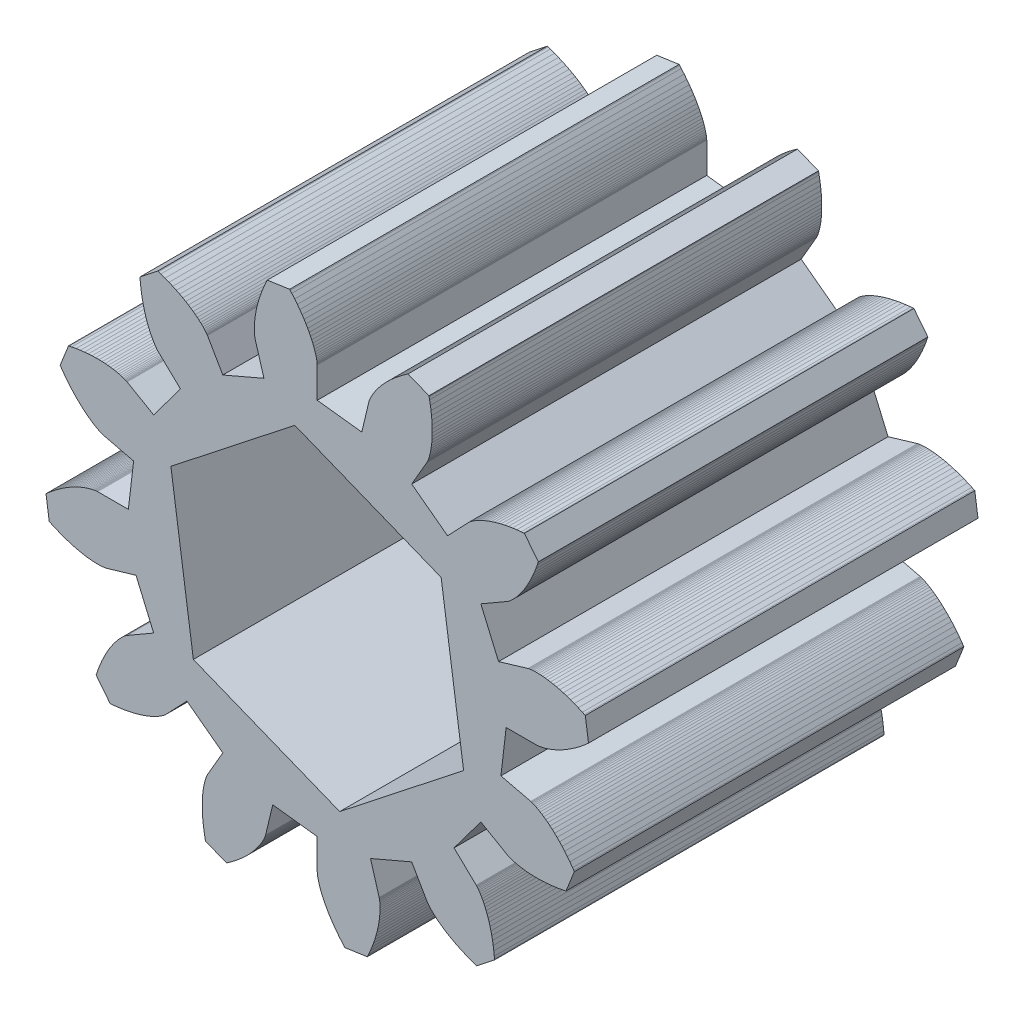
SolidWorks part; units mm, degrees
ref_plane "正面" through (0, 0, 0) normal (0, 0, 1) x (1, 0, 0)
ref_plane "平面" through (0, 0, 0) normal (0, 1, 0) x (1, 0, 0)
ref_plane "右側面" through (0, 0, 0) normal (1, 0, 0) x (0, 0, -1)
sketch "Model" plane through (0, 0, 0) normal (0, 0, 1) x (1, 0, 0)
  line L0 (2.425, 0) -> (2.8195, 0)
  line L1 (2.8195, 0) -> (2.8221, 0.0001)
  line L2 (2.8221, 0.0001) -> (2.8271, 0.0004)
  line L3 (2.8271, 0.0004) -> (2.8345, 0.0011)
  line L4 (2.8345, 0.0011) -> (2.8442, 0.0022)
  line L5 (2.8442, 0.0022) -> (2.8562, 0.004)
  line L6 (2.8562, 0.004) -> (2.8705, 0.0066)
  line L7 (2.8705, 0.0066) -> (2.8871, 0.0101)
  line L8 (2.8871, 0.0101) -> (2.9059, 0.0146)
  line L9 (2.9059, 0.0146) -> (2.9268, 0.0203)
  line L10 (2.9268, 0.0203) -> (2.9499, 0.0273)
  line L11 (2.9499, 0.0273) -> (2.975, 0.0357)
  line L12 (2.975, 0.0357) -> (3.0021, 0.0456)
  line L13 (3.0021, 0.0456) -> (3.0311, 0.0573)
  line L14 (3.0311, 0.0573) -> (3.0619, 0.0707)
  line L15 (3.0619, 0.0707) -> (3.0945, 0.086)
  line L16 (3.0945, 0.086) -> (3.1288, 0.1033)
  line L17 (3.1288, 0.1033) -> (3.1646, 0.1228)
  line L18 (3.1646, 0.1228) -> (3.202, 0.1445)
  line L19 (3.202, 0.1445) -> (3.2407, 0.1686)
  line L20 (3.2407, 0.1686) -> (3.2807, 0.195)
  line L21 (3.2807, 0.195) -> (3.3218, 0.224)
  line L22 (3.3218, 0.224) -> (3.364, 0.2556)
  line L23 (3.364, 0.2556) -> (3.4071, 0.2899)
  line L24 (3.4071, 0.2899) -> (3.451, 0.327)
  line L25 (3.451, 0.327) -> (3.4733, 0.3466)
  line L26 (3.4733, 0.3466) -> (3.4788, 0.3516)
  line L27 (3.4788, 0.3516) -> (3.4816, 0.3542)
  line L28 (3.4816, 0.3542) -> (3.482, 0.3545)
  line L29 (3.482, 0.3545) -> (3.4407, 0.6415)
  line L30 (3.4407, 0.6415) -> (3.4403, 0.6417)
  line L31 (3.4403, 0.6417) -> (3.4369, 0.6434)
  line L32 (3.4369, 0.6434) -> (3.4301, 0.6467)
  line L33 (3.4301, 0.6467) -> (3.4033, 0.6593)
  line L34 (3.4033, 0.6593) -> (3.3508, 0.6826)
  line L35 (3.3508, 0.6826) -> (3.2998, 0.7035)
  line L36 (3.2998, 0.7035) -> (3.2504, 0.722)
  line L37 (3.2504, 0.722) -> (3.2028, 0.7384)
  line L38 (3.2028, 0.7384) -> (3.157, 0.7526)
  line L39 (3.157, 0.7526) -> (3.1132, 0.7649)
  line L40 (3.1132, 0.7649) -> (3.0712, 0.7753)
  line L41 (3.0712, 0.7753) -> (3.0314, 0.7839)
  line L42 (3.0314, 0.7839) -> (2.9937, 0.791)
  line L43 (2.9937, 0.791) -> (2.9581, 0.7966)
  line L44 (2.9581, 0.7966) -> (2.9247, 0.8008)
  line L45 (2.9247, 0.8008) -> (2.8936, 0.8039)
  line L46 (2.8936, 0.8039) -> (2.8648, 0.8059)
  line L47 (2.8648, 0.8059) -> (2.8384, 0.8069)
  line L48 (2.8384, 0.8069) -> (2.8143, 0.8072)
  line L49 (2.8143, 0.8072) -> (2.7926, 0.8068)
  line L50 (2.7926, 0.8068) -> (2.7733, 0.8059)
  line L51 (2.7733, 0.8059) -> (2.7564, 0.8046)
  line L52 (2.7564, 0.8046) -> (2.7419, 0.8031)
  line L53 (2.7419, 0.8031) -> (2.7299, 0.8014)
  line L54 (2.7299, 0.8014) -> (2.7202, 0.7998)
  line L55 (2.7202, 0.7998) -> (2.7129, 0.7984)
  line L56 (2.7129, 0.7984) -> (2.7081, 0.7973)
  line L57 (2.7081, 0.7973) -> (2.7055, 0.7967)
  line L58 (2.7055, 0.7967) -> (2.3274, 0.684)
  line L59 (2.3274, 0.684) -> (2.1001, 1.2125)
  line L60 (2.1001, 1.2125) -> (2.4418, 1.4097)
  line L61 (2.4418, 1.4097) -> (2.444, 1.4111)
  line L62 (2.444, 1.4111) -> (2.4482, 1.4139)
  line L63 (2.4482, 1.4139) -> (2.4542, 1.4182)
  line L64 (2.4542, 1.4182) -> (2.462, 1.424)
  line L65 (2.462, 1.424) -> (2.4715, 1.4316)
  line L66 (2.4715, 1.4316) -> (2.4827, 1.441)
  line L67 (2.4827, 1.441) -> (2.4953, 1.4523)
  line L68 (2.4953, 1.4523) -> (2.5093, 1.4656)
  line L69 (2.5093, 1.4656) -> (2.5246, 1.481)
  line L70 (2.5246, 1.481) -> (2.5411, 1.4986)
  line L71 (2.5411, 1.4986) -> (2.5586, 1.5184)
  line L72 (2.5586, 1.5184) -> (2.5771, 1.5406)
  line L73 (2.5771, 1.5406) -> (2.5964, 1.5651)
  line L74 (2.5964, 1.5651) -> (2.6164, 1.5922)
  line L75 (2.6164, 1.5922) -> (2.637, 1.6218)
  line L76 (2.637, 1.6218) -> (2.658, 1.6539)
  line L77 (2.658, 1.6539) -> (2.6793, 1.6887)
  line L78 (2.6793, 1.6887) -> (2.7007, 1.7261)
  line L79 (2.7007, 1.7261) -> (2.7222, 1.7663)
  line L80 (2.7222, 1.7663) -> (2.7436, 1.8092)
  line L81 (2.7436, 1.8092) -> (2.7648, 1.8549)
  line L82 (2.7648, 1.8549) -> (2.7855, 1.9034)
  line L83 (2.7855, 1.9034) -> (2.8057, 1.9546)
  line L84 (2.8057, 1.9546) -> (2.8252, 2.0087)
  line L85 (2.8252, 2.0087) -> (2.8346, 2.0368)
  line L86 (2.8346, 2.0368) -> (2.837, 2.0439)
  line L87 (2.837, 2.0439) -> (2.8381, 2.0475)
  line L88 (2.8381, 2.0475) -> (2.8382, 2.048)
  line L89 (2.8382, 2.048) -> (2.659, 2.2759)
  line L90 (2.659, 2.2759) -> (2.6585, 2.2759)
  line L91 (2.6585, 2.2759) -> (2.6547, 2.2756)
  line L92 (2.6547, 2.2756) -> (2.6473, 2.275)
  line L93 (2.6473, 2.275) -> (2.6177, 2.2725)
  line L94 (2.6177, 2.2725) -> (2.5606, 2.2663)
  line L95 (2.5606, 2.2663) -> (2.506, 2.2588)
  line L96 (2.506, 2.2588) -> (2.454, 2.25)
  line L97 (2.454, 2.25) -> (2.4046, 2.2403)
  line L98 (2.4046, 2.2403) -> (2.3579, 2.2296)
  line L99 (2.3579, 2.2296) -> (2.3138, 2.2182)
  line L100 (2.3138, 2.2182) -> (2.2723, 2.2061)
  line L101 (2.2723, 2.2061) -> (2.2335, 2.1936)
  line L102 (2.2335, 2.1936) -> (2.1973, 2.1808)
  line L103 (2.1973, 2.1808) -> (2.1637, 2.1678)
  line L104 (2.1637, 2.1678) -> (2.1327, 2.1547)
  line L105 (2.1327, 2.1547) -> (2.1043, 2.1417)
  line L106 (2.1043, 2.1417) -> (2.0784, 2.129)
  line L107 (2.0784, 2.129) -> (2.055, 2.1166)
  line L108 (2.055, 2.1166) -> (2.034, 2.1048)
  line L109 (2.034, 2.1048) -> (2.0154, 2.0935)
  line L110 (2.0154, 2.0935) -> (1.9992, 2.083)
  line L111 (1.9992, 2.083) -> (1.9853, 2.0735)
  line L112 (1.9853, 2.0735) -> (1.9735, 2.0649)
  line L113 (1.9735, 2.0649) -> (1.9639, 2.0574)
  line L114 (1.9639, 2.0574) -> (1.9564, 2.0512)
  line L115 (1.9564, 2.0512) -> (1.9508, 2.0463)
  line L116 (1.9508, 2.0463) -> (1.9471, 2.0429)
  line L117 (1.9471, 2.0429) -> (1.9452, 2.0411)
  line L118 (1.9452, 2.0411) -> (1.673, 1.7556)
  line L119 (1.673, 1.7556) -> (1.2123, 2.1002)
  line L120 (1.2123, 2.1002) -> (1.4098, 2.4417)
  line L121 (1.4098, 2.4417) -> (1.411, 2.4441)
  line L122 (1.411, 2.4441) -> (1.4132, 2.4485)
  line L123 (1.4132, 2.4485) -> (1.4163, 2.4553)
  line L124 (1.4163, 2.4553) -> (1.4202, 2.4643)
  line L125 (1.4202, 2.4643) -> (1.4246, 2.4756)
  line L126 (1.4246, 2.4756) -> (1.4295, 2.4893)
  line L127 (1.4295, 2.4893) -> (1.4348, 2.5054)
  line L128 (1.4348, 2.5054) -> (1.4403, 2.5239)
  line L129 (1.4403, 2.5239) -> (1.4458, 2.5449)
  line L130 (1.4458, 2.5449) -> (1.4513, 2.5683)
  line L131 (1.4513, 2.5683) -> (1.4566, 2.5943)
  line L132 (1.4566, 2.5943) -> (1.4615, 2.6227)
  line L133 (1.4615, 2.6227) -> (1.466, 2.6536)
  line L134 (1.466, 2.6536) -> (1.4698, 2.6871)
  line L135 (1.4698, 2.6871) -> (1.4728, 2.723)
  line L136 (1.4728, 2.723) -> (1.4749, 2.7613)
  line L137 (1.4749, 2.7613) -> (1.476, 2.8021)
  line L138 (1.476, 2.8021) -> (1.4758, 2.8452)
  line L139 (1.4758, 2.8452) -> (1.4744, 2.8908)
  line L140 (1.4744, 2.8908) -> (1.4714, 2.9386)
  line L141 (1.4714, 2.9386) -> (1.4669, 2.9888)
  line L142 (1.4669, 2.9888) -> (1.4606, 3.0411)
  line L143 (1.4606, 3.0411) -> (1.4525, 3.0956)
  line L144 (1.4525, 3.0956) -> (1.4423, 3.1522)
  line L145 (1.4423, 3.1522) -> (1.4365, 3.1812)
  line L146 (1.4365, 3.1812) -> (1.4349, 3.1886)
  line L147 (1.4349, 3.1886) -> (1.4341, 3.1923)
  line L148 (1.4341, 3.1923) -> (1.434, 3.1928)
  line L149 (1.434, 3.1928) -> (1.1648, 3.3005)
  line L150 (1.1648, 3.3005) -> (1.1644, 3.3002)
  line L151 (1.1644, 3.3002) -> (1.1613, 3.2981)
  line L152 (1.1613, 3.2981) -> (1.1551, 3.2939)
  line L153 (1.1551, 3.2939) -> (1.1307, 3.277)
  line L154 (1.1307, 3.277) -> (1.0843, 3.2431)
  line L155 (1.0843, 3.2431) -> (1.0407, 3.2093)
  line L156 (1.0407, 3.2093) -> (1, 3.1758)
  line L157 (1, 3.1758) -> (0.9621, 3.1427)
  line L158 (0.9621, 3.1427) -> (0.9269, 3.1102)
  line L159 (0.9269, 3.1102) -> (0.8944, 3.0783)
  line L160 (0.8944, 3.0783) -> (0.8644, 3.0472)
  line L161 (0.8644, 3.0472) -> (0.837, 3.017)
  line L162 (0.837, 3.017) -> (0.8121, 2.9878)
  line L163 (0.8121, 2.9878) -> (0.7895, 2.9597)
  line L164 (0.7895, 2.9597) -> (0.7691, 2.933)
  line L165 (0.7691, 2.933) -> (0.7509, 2.9075)
  line L166 (0.7509, 2.9075) -> (0.7348, 2.8836)
  line L167 (0.7348, 2.8836) -> (0.7207, 2.8612)
  line L168 (0.7207, 2.8612) -> (0.7085, 2.8404)
  line L169 (0.7085, 2.8404) -> (0.698, 2.8214)
  line L170 (0.698, 2.8214) -> (0.6891, 2.8043)
  line L171 (0.6891, 2.8043) -> (0.6818, 2.789)
  line L172 (0.6818, 2.789) -> (0.6759, 2.7757)
  line L173 (0.6759, 2.7757) -> (0.6713, 2.7644)
  line L174 (0.6713, 2.7644) -> (0.6679, 2.7553)
  line L175 (0.6679, 2.7553) -> (0.6655, 2.7483)
  line L176 (0.6655, 2.7483) -> (0.664, 2.7435)
  line L177 (0.664, 2.7435) -> (0.6633, 2.741)
  line L178 (0.6633, 2.741) -> (0.5713, 2.3573)
  line L179 (0.5713, 2.3573) -> (0, 2.425)
  line L180 (0, 2.425) -> (0, 2.8195)
  line L181 (0, 2.8195) -> (-0.0001, 2.8221)
  line L182 (-0.0001, 2.8221) -> (-0.0004, 2.8271)
  line L183 (-0.0004, 2.8271) -> (-0.0011, 2.8345)
  line L184 (-0.0011, 2.8345) -> (-0.0022, 2.8442)
  line L185 (-0.0022, 2.8442) -> (-0.004, 2.8562)
  line L186 (-0.004, 2.8562) -> (-0.0066, 2.8705)
  line L187 (-0.0066, 2.8705) -> (-0.0101, 2.8871)
  line L188 (-0.0101, 2.8871) -> (-0.0146, 2.9059)
  line L189 (-0.0146, 2.9059) -> (-0.0203, 2.9268)
  line L190 (-0.0203, 2.9268) -> (-0.0273, 2.9499)
  line L191 (-0.0273, 2.9499) -> (-0.0357, 2.975)
  line L192 (-0.0357, 2.975) -> (-0.0456, 3.0021)
  line L193 (-0.0456, 3.0021) -> (-0.0573, 3.0311)
  line L194 (-0.0573, 3.0311) -> (-0.0707, 3.0619)
  line L195 (-0.0707, 3.0619) -> (-0.086, 3.0945)
  line L196 (-0.086, 3.0945) -> (-0.1034, 3.1288)
  line L197 (-0.1034, 3.1288) -> (-0.1228, 3.1646)
  line L198 (-0.1228, 3.1646) -> (-0.1445, 3.202)
  line L199 (-0.1445, 3.202) -> (-0.1686, 3.2407)
  line L200 (-0.1686, 3.2407) -> (-0.195, 3.2807)
  line L201 (-0.195, 3.2807) -> (-0.224, 3.3218)
  line L202 (-0.224, 3.3218) -> (-0.2556, 3.364)
  line L203 (-0.2556, 3.364) -> (-0.2899, 3.4071)
  line L204 (-0.2899, 3.4071) -> (-0.327, 3.451)
  line L205 (-0.327, 3.451) -> (-0.3466, 3.4733)
  line L206 (-0.3466, 3.4733) -> (-0.3516, 3.4788)
  line L207 (-0.3516, 3.4788) -> (-0.3542, 3.4816)
  line L208 (-0.3542, 3.4816) -> (-0.3545, 3.482)
  line L209 (-0.3545, 3.482) -> (-0.6415, 3.4407)
  line L210 (-0.6415, 3.4407) -> (-0.6418, 3.4403)
  line L211 (-0.6418, 3.4403) -> (-0.6434, 3.4369)
  line L212 (-0.6434, 3.4369) -> (-0.6467, 3.4301)
  line L213 (-0.6467, 3.4301) -> (-0.6593, 3.4033)
  line L214 (-0.6593, 3.4033) -> (-0.6826, 3.3508)
  line L215 (-0.6826, 3.3508) -> (-0.7035, 3.2998)
  line L216 (-0.7035, 3.2998) -> (-0.7221, 3.2505)
  line L217 (-0.7221, 3.2505) -> (-0.7385, 3.2029)
  line L218 (-0.7385, 3.2029) -> (-0.7527, 3.1571)
  line L219 (-0.7527, 3.1571) -> (-0.765, 3.1132)
  line L220 (-0.765, 3.1132) -> (-0.7754, 3.0713)
  line L221 (-0.7754, 3.0713) -> (-0.7841, 3.0314)
  line L222 (-0.7841, 3.0314) -> (-0.7912, 2.9937)
  line L223 (-0.7912, 2.9937) -> (-0.7968, 2.9581)
  line L224 (-0.7968, 2.9581) -> (-0.8011, 2.9248)
  line L225 (-0.8011, 2.9248) -> (-0.8041, 2.8937)
  line L226 (-0.8041, 2.8937) -> (-0.8061, 2.8649)
  line L227 (-0.8061, 2.8649) -> (-0.8072, 2.8384)
  line L228 (-0.8072, 2.8384) -> (-0.8074, 2.8143)
  line L229 (-0.8074, 2.8143) -> (-0.8071, 2.7926)
  line L230 (-0.8071, 2.7926) -> (-0.8061, 2.7733)
  line L231 (-0.8061, 2.7733) -> (-0.8049, 2.7564)
  line L232 (-0.8049, 2.7564) -> (-0.8033, 2.742)
  line L233 (-0.8033, 2.742) -> (-0.8017, 2.7299)
  line L234 (-0.8017, 2.7299) -> (-0.8001, 2.7203)
  line L235 (-0.8001, 2.7203) -> (-0.7987, 2.713)
  line L236 (-0.7987, 2.713) -> (-0.7976, 2.7081)
  line L237 (-0.7976, 2.7081) -> (-0.797, 2.7056)
  line L238 (-0.797, 2.7056) -> (-0.6841, 2.3276)
  line L239 (-0.6841, 2.3276) -> (-1.2125, 2.1001)
  line L240 (-1.2125, 2.1001) -> (-1.4097, 2.4418)
  line L241 (-1.4097, 2.4418) -> (-1.4111, 2.444)
  line L242 (-1.4111, 2.444) -> (-1.4139, 2.4482)
  line L243 (-1.4139, 2.4482) -> (-1.4182, 2.4542)
  line L244 (-1.4182, 2.4542) -> (-1.424, 2.462)
  line L245 (-1.424, 2.462) -> (-1.4316, 2.4715)
  line L246 (-1.4316, 2.4715) -> (-1.441, 2.4827)
  line L247 (-1.441, 2.4827) -> (-1.4523, 2.4953)
  line L248 (-1.4523, 2.4953) -> (-1.4656, 2.5093)
  line L249 (-1.4656, 2.5093) -> (-1.481, 2.5246)
  line L250 (-1.481, 2.5246) -> (-1.4986, 2.5411)
  line L251 (-1.4986, 2.5411) -> (-1.5184, 2.5586)
  line L252 (-1.5184, 2.5586) -> (-1.5406, 2.5771)
  line L253 (-1.5406, 2.5771) -> (-1.5652, 2.5964)
  line L254 (-1.5652, 2.5964) -> (-1.5922, 2.6164)
  line L255 (-1.5922, 2.6164) -> (-1.6218, 2.637)
  line L256 (-1.6218, 2.637) -> (-1.6539, 2.658)
  line L257 (-1.6539, 2.658) -> (-1.6887, 2.6793)
  line L258 (-1.6887, 2.6793) -> (-1.7261, 2.7007)
  line L259 (-1.7261, 2.7007) -> (-1.7663, 2.7222)
  line L260 (-1.7663, 2.7222) -> (-1.8092, 2.7436)
  line L261 (-1.8092, 2.7436) -> (-1.8549, 2.7648)
  line L262 (-1.8549, 2.7648) -> (-1.9034, 2.7855)
  line L263 (-1.9034, 2.7855) -> (-1.9546, 2.8057)
  line L264 (-1.9546, 2.8057) -> (-2.0087, 2.8252)
  line L265 (-2.0087, 2.8252) -> (-2.0368, 2.8346)
  line L266 (-2.0368, 2.8346) -> (-2.0439, 2.837)
  line L267 (-2.0439, 2.837) -> (-2.0475, 2.8381)
  line L268 (-2.0475, 2.8381) -> (-2.048, 2.8382)
  line L269 (-2.048, 2.8382) -> (-2.2759, 2.6585)
  line L270 (-2.2759, 2.659) -> (-2.2759, 2.6585)
  line L271 (-2.2759, 2.6585) -> (-2.2756, 2.6547)
  line L272 (-2.2756, 2.6547) -> (-2.2751, 2.6473)
  line L273 (-2.2751, 2.6473) -> (-2.2725, 2.6177)
  line L274 (-2.2725, 2.6177) -> (-2.2663, 2.5606)
  line L275 (-2.2663, 2.5606) -> (-2.2588, 2.506)
  line L276 (-2.2588, 2.506) -> (-2.25, 2.454)
  line L277 (-2.25, 2.454) -> (-2.2403, 2.4046)
  line L278 (-2.2403, 2.4046) -> (-2.2296, 2.3579)
  line L279 (-2.2296, 2.3579) -> (-2.2182, 2.3138)
  line L280 (-2.2182, 2.3138) -> (-2.2061, 2.2723)
  line L281 (-2.2061, 2.2723) -> (-2.1936, 2.2335)
  line L282 (-2.1936, 2.2335) -> (-2.1808, 2.1973)
  line L283 (-2.1808, 2.1973) -> (-2.1678, 2.1637)
  line L284 (-2.1678, 2.1637) -> (-2.1547, 2.1327)
  line L285 (-2.1547, 2.1327) -> (-2.1417, 2.1043)
  line L286 (-2.1417, 2.1043) -> (-2.129, 2.0784)
  line L287 (-2.129, 2.0784) -> (-2.1166, 2.055)
  line L288 (-2.1166, 2.055) -> (-2.1048, 2.034)
  line L289 (-2.1048, 2.034) -> (-2.0935, 2.0154)
  line L290 (-2.0935, 2.0154) -> (-2.0831, 1.9992)
  line L291 (-2.0831, 1.9992) -> (-2.0735, 1.9853)
  line L292 (-2.0735, 1.9853) -> (-2.0649, 1.9735)
  line L293 (-2.0649, 1.9735) -> (-2.0574, 1.9639)
  line L294 (-2.0574, 1.9639) -> (-2.0512, 1.9564)
  line L295 (-2.0512, 1.9564) -> (-2.0463, 1.9508)
  line L296 (-2.0463, 1.9508) -> (-2.0429, 1.9471)
  line L297 (-2.0429, 1.9471) -> (-2.0411, 1.9452)
  line L298 (-2.0411, 1.9452) -> (-1.7556, 1.673)
  line L299 (-1.7556, 1.673) -> (-2.1002, 1.2123)
  line L300 (-2.1002, 1.2123) -> (-2.4418, 1.4097)
  line L301 (-2.4418, 1.4097) -> (-2.4441, 1.411)
  line L302 (-2.4441, 1.411) -> (-2.4486, 1.4132)
  line L303 (-2.4486, 1.4132) -> (-2.4553, 1.4163)
  line L304 (-2.4553, 1.4163) -> (-2.4643, 1.4202)
  line L305 (-2.4643, 1.4202) -> (-2.4756, 1.4246)
  line L306 (-2.4756, 1.4246) -> (-2.4893, 1.4295)
  line L307 (-2.4893, 1.4295) -> (-2.5054, 1.4348)
  line L308 (-2.5054, 1.4348) -> (-2.5239, 1.4403)
  line L309 (-2.5239, 1.4403) -> (-2.5449, 1.4458)
  line L310 (-2.5449, 1.4458) -> (-2.5683, 1.4513)
  line L311 (-2.5683, 1.4513) -> (-2.5943, 1.4566)
  line L312 (-2.5943, 1.4566) -> (-2.6227, 1.4615)
  line L313 (-2.6227, 1.4615) -> (-2.6537, 1.466)
  line L314 (-2.6537, 1.466) -> (-2.6871, 1.4698)
  line L315 (-2.6871, 1.4698) -> (-2.723, 1.4728)
  line L316 (-2.723, 1.4728) -> (-2.7613, 1.4749)
  line L317 (-2.7613, 1.4749) -> (-2.8021, 1.476)
  line L318 (-2.8021, 1.476) -> (-2.8453, 1.4758)
  line L319 (-2.8453, 1.4758) -> (-2.8908, 1.4744)
  line L320 (-2.8908, 1.4744) -> (-2.9386, 1.4714)
  line L321 (-2.9386, 1.4714) -> (-2.9888, 1.4669)
  line L322 (-2.9888, 1.4669) -> (-3.0411, 1.4606)
  line L323 (-3.0411, 1.4606) -> (-3.0956, 1.4525)
  line L324 (-3.0956, 1.4525) -> (-3.1522, 1.4423)
  line L325 (-3.1522, 1.4423) -> (-3.1812, 1.4365)
  line L326 (-3.1812, 1.4365) -> (-3.1886, 1.4349)
  line L327 (-3.1886, 1.4349) -> (-3.1923, 1.4341)
  line L328 (-3.1923, 1.4341) -> (-3.1928, 1.4339)
  line L329 (-3.1928, 1.4339) -> (-3.3005, 1.1648)
  line L330 (-3.3005, 1.1648) -> (-3.3002, 1.1644)
  line L331 (-3.3002, 1.1644) -> (-3.2981, 1.1613)
  line L332 (-3.2981, 1.1613) -> (-3.2939, 1.1551)
  line L333 (-3.2939, 1.1551) -> (-3.277, 1.1307)
  line L334 (-3.277, 1.1307) -> (-3.2431, 1.0843)
  line L335 (-3.2431, 1.0843) -> (-3.2093, 1.0407)
  line L336 (-3.2093, 1.0407) -> (-3.1758, 1)
  line L337 (-3.1758, 1) -> (-3.1427, 0.9621)
  line L338 (-3.1427, 0.9621) -> (-3.1102, 0.9269)
  line L339 (-3.1102, 0.9269) -> (-3.0783, 0.8944)
  line L340 (-3.0783, 0.8944) -> (-3.0472, 0.8644)
  line L341 (-3.0472, 0.8644) -> (-3.017, 0.837)
  line L342 (-3.017, 0.837) -> (-2.9878, 0.8121)
  line L343 (-2.9878, 0.8121) -> (-2.9597, 0.7894)
  line L344 (-2.9597, 0.7894) -> (-2.933, 0.7691)
  line L345 (-2.933, 0.7691) -> (-2.9075, 0.7509)
  line L346 (-2.9075, 0.7509) -> (-2.8836, 0.7348)
  line L347 (-2.8836, 0.7348) -> (-2.8612, 0.7207)
  line L348 (-2.8612, 0.7207) -> (-2.8404, 0.7085)
  line L349 (-2.8404, 0.7085) -> (-2.8214, 0.698)
  line L350 (-2.8214, 0.698) -> (-2.8043, 0.6891)
  line L351 (-2.8043, 0.6891) -> (-2.789, 0.6818)
  line L352 (-2.789, 0.6818) -> (-2.7757, 0.6759)
  line L353 (-2.7757, 0.6759) -> (-2.7644, 0.6713)
  line L354 (-2.7644, 0.6713) -> (-2.7553, 0.6679)
  line L355 (-2.7553, 0.6679) -> (-2.7483, 0.6655)
  line L356 (-2.7483, 0.6655) -> (-2.7435, 0.664)
  line L357 (-2.7435, 0.664) -> (-2.741, 0.6633)
  line L358 (-2.741, 0.6633) -> (-2.3573, 0.5713)
  line L359 (-2.3573, 0.5713) -> (-2.425, 0)
  line L360 (-2.425, 0) -> (-2.8195, 0)
  line L361 (-2.8195, 0) -> (-2.8221, -0.0001)
  line L362 (-2.8221, -0.0001) -> (-2.8271, -0.0004)
  line L363 (-2.8271, -0.0004) -> (-2.8345, -0.0011)
  line L364 (-2.8345, -0.0011) -> (-2.8442, -0.0022)
  line L365 (-2.8442, -0.0022) -> (-2.8562, -0.0041)
  line L366 (-2.8562, -0.0041) -> (-2.8705, -0.0066)
  line L367 (-2.8705, -0.0066) -> (-2.8871, -0.0101)
  line L368 (-2.8871, -0.0101) -> (-2.9059, -0.0146)
  line L369 (-2.9059, -0.0146) -> (-2.9268, -0.0203)
  line L370 (-2.9268, -0.0203) -> (-2.9499, -0.0273)
  line L371 (-2.9499, -0.0273) -> (-2.975, -0.0357)
  line L372 (-2.975, -0.0357) -> (-3.0021, -0.0456)
  line L373 (-3.0021, -0.0456) -> (-3.0311, -0.0573)
  line L374 (-3.0311, -0.0573) -> (-3.0619, -0.0707)
  line L375 (-3.0619, -0.0707) -> (-3.0945, -0.086)
  line L376 (-3.0945, -0.086) -> (-3.1288, -0.1034)
  line L377 (-3.1288, -0.1034) -> (-3.1646, -0.1228)
  line L378 (-3.1646, -0.1228) -> (-3.202, -0.1445)
  line L379 (-3.202, -0.1445) -> (-3.2407, -0.1686)
  line L380 (-3.2407, -0.1686) -> (-3.2807, -0.195)
  line L381 (-3.2807, -0.195) -> (-3.3218, -0.224)
  line L382 (-3.3218, -0.224) -> (-3.364, -0.2556)
  line L383 (-3.364, -0.2556) -> (-3.4071, -0.2899)
  line L384 (-3.4071, -0.2899) -> (-3.451, -0.327)
  line L385 (-3.451, -0.327) -> (-3.4733, -0.3466)
  line L386 (-3.4733, -0.3466) -> (-3.4788, -0.3516)
  line L387 (-3.4788, -0.3516) -> (-3.4816, -0.3542)
  line L388 (-3.4816, -0.3542) -> (-3.482, -0.3545)
  line L389 (-3.482, -0.3545) -> (-3.4407, -0.6415)
  line L390 (-3.4407, -0.6415) -> (-3.4403, -0.6418)
  line L391 (-3.4403, -0.6418) -> (-3.4369, -0.6434)
  line L392 (-3.4369, -0.6434) -> (-3.4301, -0.6467)
  line L393 (-3.4301, -0.6467) -> (-3.4033, -0.6593)
  line L394 (-3.4033, -0.6593) -> (-3.3507, -0.6824)
  line L395 (-3.3507, -0.6824) -> (-3.2996, -0.7031)
  line L396 (-3.2996, -0.7031) -> (-3.2502, -0.7215)
  line L397 (-3.2502, -0.7215) -> (-3.2026, -0.7378)
  line L398 (-3.2026, -0.7378) -> (-3.1568, -0.7519)
  line L399 (-3.1568, -0.7519) -> (-3.1129, -0.764)
  line L400 (-3.1129, -0.764) -> (-3.0709, -0.7743)
  line L401 (-3.0709, -0.7743) -> (-3.0311, -0.7829)
  line L402 (-3.0311, -0.7829) -> (-2.9933, -0.7899)
  line L403 (-2.9933, -0.7899) -> (-2.9577, -0.7954)
  line L404 (-2.9577, -0.7954) -> (-2.9243, -0.7996)
  line L405 (-2.9243, -0.7996) -> (-2.8932, -0.8026)
  line L406 (-2.8932, -0.8026) -> (-2.8644, -0.8045)
  line L407 (-2.8644, -0.8045) -> (-2.838, -0.8055)
  line L408 (-2.838, -0.8055) -> (-2.8139, -0.8057)
  line L409 (-2.8139, -0.8057) -> (-2.7922, -0.8052)
  line L410 (-2.7922, -0.8052) -> (-2.7729, -0.8042)
  line L411 (-2.7729, -0.8042) -> (-2.756, -0.8029)
  line L412 (-2.756, -0.8029) -> (-2.7415, -0.8013)
  line L413 (-2.7415, -0.8013) -> (-2.7295, -0.7997)
  line L414 (-2.7295, -0.7997) -> (-2.7198, -0.7981)
  line L415 (-2.7198, -0.7981) -> (-2.7126, -0.7966)
  line L416 (-2.7126, -0.7966) -> (-2.7077, -0.7955)
  line L417 (-2.7077, -0.7955) -> (-2.7051, -0.7949)
  line L418 (-2.7051, -0.7949) -> (-2.3266, -0.6837)
  line L419 (-2.3266, -0.6837) -> (-2.1001, -1.2125)
  line L420 (-2.1001, -1.2125) -> (-2.4418, -1.4097)
  line L421 (-2.4418, -1.4097) -> (-2.444, -1.4111)
  line L422 (-2.444, -1.4111) -> (-2.4482, -1.4139)
  line L423 (-2.4482, -1.4139) -> (-2.4542, -1.4182)
  line L424 (-2.4542, -1.4182) -> (-2.462, -1.424)
  line L425 (-2.462, -1.424) -> (-2.4715, -1.4316)
  line L426 (-2.4715, -1.4316) -> (-2.4827, -1.441)
  line L427 (-2.4827, -1.441) -> (-2.4953, -1.4523)
  line L428 (-2.4953, -1.4523) -> (-2.5093, -1.4656)
  line L429 (-2.5093, -1.4656) -> (-2.5246, -1.481)
  line L430 (-2.5246, -1.481) -> (-2.5411, -1.4986)
  line L431 (-2.5411, -1.4986) -> (-2.5586, -1.5184)
  line L432 (-2.5586, -1.5184) -> (-2.5771, -1.5406)
  line L433 (-2.5771, -1.5406) -> (-2.5964, -1.5652)
  line L434 (-2.5964, -1.5652) -> (-2.6164, -1.5922)
  line L435 (-2.6164, -1.5922) -> (-2.637, -1.6218)
  line L436 (-2.637, -1.6218) -> (-2.658, -1.6539)
  line L437 (-2.658, -1.6539) -> (-2.6793, -1.6887)
  line L438 (-2.6793, -1.6887) -> (-2.7007, -1.7261)
  line L439 (-2.7007, -1.7261) -> (-2.7222, -1.7663)
  line L440 (-2.7222, -1.7663) -> (-2.7436, -1.8092)
  line L441 (-2.7436, -1.8092) -> (-2.7648, -1.8549)
  line L442 (-2.7648, -1.8549) -> (-2.7855, -1.9034)
  line L443 (-2.7855, -1.9034) -> (-2.8057, -1.9546)
  line L444 (-2.8057, -1.9546) -> (-2.8252, -2.0087)
  line L445 (-2.8252, -2.0087) -> (-2.8346, -2.0368)
  line L446 (-2.8346, -2.0368) -> (-2.837, -2.044)
  line L447 (-2.837, -2.044) -> (-2.8381, -2.0475)
  line L448 (-2.8381, -2.0475) -> (-2.8382, -2.048)
  line L449 (-2.8382, -2.048) -> (-2.659, -2.2759)
  line L450 (-2.659, -2.2759) -> (-2.6585, -2.2759)
  line L451 (-2.6585, -2.2759) -> (-2.6547, -2.2756)
  line L452 (-2.6547, -2.2756) -> (-2.6473, -2.2751)
  line L453 (-2.6473, -2.2751) -> (-2.6177, -2.2725)
  line L454 (-2.6177, -2.2725) -> (-2.5606, -2.2663)
  line L455 (-2.5606, -2.2663) -> (-2.506, -2.2588)
  line L456 (-2.506, -2.2588) -> (-2.454, -2.25)
  line L457 (-2.454, -2.25) -> (-2.4046, -2.2403)
  line L458 (-2.4046, -2.2403) -> (-2.3579, -2.2296)
  line L459 (-2.3579, -2.2296) -> (-2.3138, -2.2182)
  line L460 (-2.3138, -2.2182) -> (-2.2723, -2.2061)
  line L461 (-2.2723, -2.2061) -> (-2.2335, -2.1936)
  line L462 (-2.2335, -2.1936) -> (-2.1973, -2.1808)
  line L463 (-2.1973, -2.1808) -> (-2.1637, -2.1678)
  line L464 (-2.1637, -2.1678) -> (-2.1327, -2.1547)
  line L465 (-2.1327, -2.1547) -> (-2.1043, -2.1418)
  line L466 (-2.1043, -2.1418) -> (-2.0784, -2.129)
  line L467 (-2.0784, -2.129) -> (-2.055, -2.1166)
  line L468 (-2.055, -2.1166) -> (-2.034, -2.1048)
  line L469 (-2.034, -2.1048) -> (-2.0154, -2.0935)
  line L470 (-2.0154, -2.0935) -> (-1.9992, -2.0831)
  line L471 (-1.9992, -2.0831) -> (-1.9853, -2.0735)
  line L472 (-1.9853, -2.0735) -> (-1.9735, -2.0649)
  line L473 (-1.9735, -2.0649) -> (-1.9639, -2.0574)
  line L474 (-1.9639, -2.0574) -> (-1.9564, -2.0512)
  line L475 (-1.9564, -2.0512) -> (-1.9508, -2.0463)
  line L476 (-1.9508, -2.0463) -> (-1.9471, -2.0429)
  line L477 (-1.9471, -2.0429) -> (-1.9452, -2.0411)
  line L478 (-1.9452, -2.0411) -> (-1.673, -1.7556)
  line L479 (-1.673, -1.7556) -> (-1.2123, -2.1002)
  line L480 (-1.2123, -2.1002) -> (-1.4098, -2.4418)
  line L481 (-1.4098, -2.4418) -> (-1.411, -2.4441)
  line L482 (-1.411, -2.4441) -> (-1.4132, -2.4486)
  line L483 (-1.4132, -2.4486) -> (-1.4163, -2.4553)
  line L484 (-1.4163, -2.4553) -> (-1.4202, -2.4643)
  line L485 (-1.4202, -2.4643) -> (-1.4246, -2.4756)
  line L486 (-1.4246, -2.4756) -> (-1.4295, -2.4893)
  line L487 (-1.4295, -2.4893) -> (-1.4348, -2.5054)
  line L488 (-1.4348, -2.5054) -> (-1.4403, -2.5239)
  line L489 (-1.4403, -2.5239) -> (-1.4459, -2.5449)
  line L490 (-1.4459, -2.5449) -> (-1.4513, -2.5683)
  line L491 (-1.4513, -2.5683) -> (-1.4566, -2.5943)
  line L492 (-1.4566, -2.5943) -> (-1.4615, -2.6227)
  line L493 (-1.4615, -2.6227) -> (-1.466, -2.6537)
  line L494 (-1.466, -2.6537) -> (-1.4698, -2.6871)
  line L495 (-1.4698, -2.6871) -> (-1.4728, -2.723)
  line L496 (-1.4728, -2.723) -> (-1.4749, -2.7613)
  line L497 (-1.4749, -2.7613) -> (-1.476, -2.8021)
  line L498 (-1.476, -2.8021) -> (-1.4758, -2.8453)
  line L499 (-1.4758, -2.8453) -> (-1.4744, -2.8908)
  line L500 (-1.4744, -2.8908) -> (-1.4714, -2.9386)
  line L501 (-1.4714, -2.9386) -> (-1.4669, -2.9888)
  line L502 (-1.4669, -2.9888) -> (-1.4606, -3.0411)
  line L503 (-1.4606, -3.0411) -> (-1.4525, -3.0956)
  line L504 (-1.4525, -3.0956) -> (-1.4423, -3.1522)
  line L505 (-1.4423, -3.1522) -> (-1.4365, -3.1813)
  line L506 (-1.4365, -3.1813) -> (-1.4349, -3.1886)
  line L507 (-1.4349, -3.1886) -> (-1.4341, -3.1923)
  line L508 (-1.4341, -3.1923) -> (-1.434, -3.1928)
  line L509 (-1.434, -3.1928) -> (-1.1648, -3.3005)
  line L510 (-1.1648, -3.3005) -> (-1.1644, -3.3002)
  line L511 (-1.1644, -3.3002) -> (-1.1613, -3.2981)
  line L512 (-1.1613, -3.2981) -> (-1.1551, -3.2939)
  line L513 (-1.1551, -3.2939) -> (-1.1307, -3.277)
  line L514 (-1.1307, -3.277) -> (-1.0843, -3.2431)
  line L515 (-1.0843, -3.2431) -> (-1.0407, -3.2093)
  line L516 (-1.0407, -3.2093) -> (-1, -3.1758)
  line L517 (-1, -3.1758) -> (-0.9621, -3.1427)
  line L518 (-0.9621, -3.1427) -> (-0.9269, -3.1102)
  line L519 (-0.9269, -3.1102) -> (-0.8944, -3.0783)
  line L520 (-0.8944, -3.0783) -> (-0.8644, -3.0472)
  line L521 (-0.8644, -3.0472) -> (-0.837, -3.017)
  line L522 (-0.837, -3.017) -> (-0.8121, -2.9878)
  line L523 (-0.8121, -2.9878) -> (-0.7895, -2.9598)
  line L524 (-0.7895, -2.9598) -> (-0.7691, -2.933)
  line L525 (-0.7691, -2.933) -> (-0.7509, -2.9076)
  line L526 (-0.7509, -2.9076) -> (-0.7348, -2.8836)
  line L527 (-0.7348, -2.8836) -> (-0.7207, -2.8612)
  line L528 (-0.7207, -2.8612) -> (-0.7085, -2.8405)
  line L529 (-0.7085, -2.8405) -> (-0.698, -2.8214)
  line L530 (-0.698, -2.8214) -> (-0.6891, -2.8043)
  line L531 (-0.6891, -2.8043) -> (-0.6818, -2.789)
  line L532 (-0.6818, -2.789) -> (-0.6759, -2.7757)
  line L533 (-0.6759, -2.7757) -> (-0.6713, -2.7644)
  line L534 (-0.6713, -2.7644) -> (-0.6679, -2.7553)
  line L535 (-0.6679, -2.7553) -> (-0.6655, -2.7483)
  line L536 (-0.6655, -2.7483) -> (-0.664, -2.7435)
  line L537 (-0.664, -2.7435) -> (-0.6633, -2.741)
  line L538 (-0.6633, -2.741) -> (-0.5713, -2.3573)
  line L539 (-0.5713, -2.3573) -> (0, -2.425)
  line L540 (0, -2.425) -> (0, -2.8195)
  line L541 (0, -2.8195) -> (0.0001, -2.8221)
  line L542 (0.0001, -2.8221) -> (0.0004, -2.8271)
  line L543 (0.0004, -2.8271) -> (0.0011, -2.8345)
  line L544 (0.0011, -2.8345) -> (0.0022, -2.8442)
  line L545 (0.0022, -2.8442) -> (0.004, -2.8562)
  line L546 (0.004, -2.8562) -> (0.0066, -2.8705)
  line L547 (0.0066, -2.8705) -> (0.0101, -2.8871)
  line L548 (0.0101, -2.8871) -> (0.0146, -2.9059)
  line L549 (0.0146, -2.9059) -> (0.0203, -2.9268)
  line L550 (0.0203, -2.9268) -> (0.0273, -2.9499)
  line L551 (0.0273, -2.9499) -> (0.0357, -2.975)
  line L552 (0.0357, -2.975) -> (0.0456, -3.0021)
  line L553 (0.0456, -3.0021) -> (0.0573, -3.0311)
  line L554 (0.0573, -3.0311) -> (0.0707, -3.0619)
  line L555 (0.0707, -3.0619) -> (0.086, -3.0945)
  line L556 (0.086, -3.0945) -> (0.1033, -3.1288)
  line L557 (0.1033, -3.1288) -> (0.1228, -3.1646)
  line L558 (0.1228, -3.1646) -> (0.1445, -3.202)
  line L559 (0.1445, -3.202) -> (0.1686, -3.2407)
  line L560 (0.1686, -3.2407) -> (0.195, -3.2807)
  line L561 (0.195, -3.2807) -> (0.224, -3.3218)
  line L562 (0.224, -3.3218) -> (0.2556, -3.364)
  line L563 (0.2556, -3.364) -> (0.2899, -3.4071)
  line L564 (0.2899, -3.4071) -> (0.327, -3.451)
  line L565 (0.327, -3.451) -> (0.3466, -3.4733)
  line L566 (0.3466, -3.4733) -> (0.3516, -3.4788)
  line L567 (0.3516, -3.4788) -> (0.3542, -3.4816)
  line L568 (0.3542, -3.4816) -> (0.3545, -3.482)
  line L569 (0.3545, -3.482) -> (0.6415, -3.4407)
  line L570 (0.6415, -3.4407) -> (0.6417, -3.4403)
  line L571 (0.6417, -3.4403) -> (0.6434, -3.4369)
  line L572 (0.6434, -3.4369) -> (0.6467, -3.4301)
  line L573 (0.6467, -3.4301) -> (0.6593, -3.4033)
  line L574 (0.6593, -3.4033) -> (0.6826, -3.3508)
  line L575 (0.6826, -3.3508) -> (0.7035, -3.2998)
  line L576 (0.7035, -3.2998) -> (0.722, -3.2504)
  line L577 (0.722, -3.2504) -> (0.7384, -3.2028)
  line L578 (0.7384, -3.2028) -> (0.7518, -3.1568)
  line L579 (0.7518, -3.1568) -> (0.764, -3.1129)
  line L580 (0.764, -3.1129) -> (0.7744, -3.071)
  line L581 (0.7744, -3.071) -> (0.783, -3.0311)
  line L582 (0.783, -3.0311) -> (0.79, -2.9934)
  line L583 (0.79, -2.9934) -> (0.7956, -2.9578)
  line L584 (0.7956, -2.9578) -> (0.7998, -2.9244)
  line L585 (0.7998, -2.9244) -> (0.8028, -2.8933)
  line L586 (0.8028, -2.8933) -> (0.8047, -2.8645)
  line L587 (0.8047, -2.8645) -> (0.8058, -2.8381)
  line L588 (0.8058, -2.8381) -> (0.806, -2.814)
  line L589 (0.806, -2.814) -> (0.8056, -2.7923)
  line L590 (0.8056, -2.7923) -> (0.8046, -2.773)
  line L591 (0.8046, -2.773) -> (0.8033, -2.7561)
  line L592 (0.8033, -2.7561) -> (0.8018, -2.7416)
  line L593 (0.8018, -2.7416) -> (0.8001, -2.7296)
  line L594 (0.8001, -2.7296) -> (0.7985, -2.7199)
  line L595 (0.7985, -2.7199) -> (0.7971, -2.7127)
  line L596 (0.7971, -2.7127) -> (0.796, -2.7078)
  line L597 (0.796, -2.7078) -> (0.7953, -2.7052)
  line L598 (0.7953, -2.7052) -> (0.6837, -2.3268)
  line L599 (0.6837, -2.3268) -> (1.2125, -2.1001)
  line L600 (1.2125, -2.1001) -> (1.4097, -2.4418)
  line L601 (1.4097, -2.4418) -> (1.4111, -2.444)
  line L602 (1.4111, -2.444) -> (1.4139, -2.4482)
  line L603 (1.4139, -2.4482) -> (1.4182, -2.4542)
  line L604 (1.4182, -2.4542) -> (1.424, -2.462)
  line L605 (1.424, -2.462) -> (1.4316, -2.4715)
  line L606 (1.4316, -2.4715) -> (1.441, -2.4827)
  line L607 (1.441, -2.4827) -> (1.4523, -2.4953)
  line L608 (1.4523, -2.4953) -> (1.4656, -2.5093)
  line L609 (1.4656, -2.5093) -> (1.481, -2.5246)
  line L610 (1.481, -2.5246) -> (1.4986, -2.5411)
  line L611 (1.4986, -2.5411) -> (1.5184, -2.5586)
  line L612 (1.5184, -2.5586) -> (1.5406, -2.5771)
  line L613 (1.5406, -2.5771) -> (1.5651, -2.5964)
  line L614 (1.5651, -2.5964) -> (1.5922, -2.6164)
  line L615 (1.5922, -2.6164) -> (1.6218, -2.637)
  line L616 (1.6218, -2.637) -> (1.6539, -2.658)
  line L617 (1.6539, -2.658) -> (1.6887, -2.6793)
  line L618 (1.6887, -2.6793) -> (1.7261, -2.7007)
  line L619 (1.7261, -2.7007) -> (1.7663, -2.7222)
  line L620 (1.7663, -2.7222) -> (1.8092, -2.7436)
  line L621 (1.8092, -2.7436) -> (1.8549, -2.7648)
  line L622 (1.8549, -2.7648) -> (1.9034, -2.7855)
  line L623 (1.9034, -2.7855) -> (1.9546, -2.8057)
  line L624 (1.9546, -2.8057) -> (2.0087, -2.8252)
  line L625 (2.0087, -2.8252) -> (2.0368, -2.8346)
  line L626 (2.0368, -2.8346) -> (2.0439, -2.837)
  line L627 (2.0439, -2.837) -> (2.0475, -2.8381)
  line L628 (2.0475, -2.8381) -> (2.048, -2.8382)
  line L629 (2.048, -2.8382) -> (2.2759, -2.6585)
  line L630 (2.2759, -2.659) -> (2.2759, -2.6585)
  line L631 (2.2759, -2.6585) -> (2.2756, -2.6547)
  line L632 (2.2756, -2.6547) -> (2.275, -2.6473)
  line L633 (2.275, -2.6473) -> (2.2725, -2.6177)
  line L634 (2.2725, -2.6177) -> (2.2663, -2.5606)
  line L635 (2.2663, -2.5606) -> (2.2588, -2.506)
  line L636 (2.2588, -2.506) -> (2.25, -2.454)
  line L637 (2.25, -2.454) -> (2.2403, -2.4046)
  line L638 (2.2403, -2.4046) -> (2.2296, -2.3579)
  line L639 (2.2296, -2.3579) -> (2.2182, -2.3138)
  line L640 (2.2182, -2.3138) -> (2.2061, -2.2723)
  line L641 (2.2061, -2.2723) -> (2.1936, -2.2335)
  line L642 (2.1936, -2.2335) -> (2.1808, -2.1973)
  line L643 (2.1808, -2.1973) -> (2.1678, -2.1637)
  line L644 (2.1678, -2.1637) -> (2.1547, -2.1327)
  line L645 (2.1547, -2.1327) -> (2.1417, -2.1043)
  line L646 (2.1417, -2.1043) -> (2.129, -2.0784)
  line L647 (2.129, -2.0784) -> (2.1166, -2.055)
  line L648 (2.1166, -2.055) -> (2.1048, -2.034)
  line L649 (2.1048, -2.034) -> (2.0935, -2.0155)
  line L650 (2.0935, -2.0155) -> (2.0831, -1.9992)
  line L651 (2.0831, -1.9992) -> (2.0735, -1.9853)
  line L652 (2.0735, -1.9853) -> (2.0649, -1.9735)
  line L653 (2.0649, -1.9735) -> (2.0574, -1.9639)
  line L654 (2.0574, -1.9639) -> (2.0512, -1.9564)
  line L655 (2.0512, -1.9564) -> (2.0463, -1.9508)
  line L656 (2.0463, -1.9508) -> (2.0429, -1.9471)
  line L657 (2.0429, -1.9471) -> (2.0411, -1.9452)
  line L658 (2.0411, -1.9452) -> (1.7556, -1.673)
  line L659 (1.7556, -1.673) -> (2.1002, -1.2123)
  line L660 (2.1002, -1.2123) -> (2.4418, -1.4098)
  line L661 (2.4418, -1.4098) -> (2.4441, -1.411)
  line L662 (2.4441, -1.411) -> (2.4486, -1.4132)
  line L663 (2.4486, -1.4132) -> (2.4553, -1.4163)
  line L664 (2.4553, -1.4163) -> (2.4643, -1.4202)
  line L665 (2.4643, -1.4202) -> (2.4756, -1.4246)
  line L666 (2.4756, -1.4246) -> (2.4893, -1.4295)
  line L667 (2.4893, -1.4295) -> (2.5054, -1.4348)
  line L668 (2.5054, -1.4348) -> (2.5239, -1.4403)
  line L669 (2.5239, -1.4403) -> (2.5449, -1.4459)
  line L670 (2.5449, -1.4459) -> (2.5683, -1.4513)
  line L671 (2.5683, -1.4513) -> (2.5943, -1.4566)
  line L672 (2.5943, -1.4566) -> (2.6227, -1.4615)
  line L673 (2.6227, -1.4615) -> (2.6536, -1.466)
  line L674 (2.6536, -1.466) -> (2.6871, -1.4698)
  line L675 (2.6871, -1.4698) -> (2.723, -1.4728)
  line L676 (2.723, -1.4728) -> (2.7613, -1.4749)
  line L677 (2.7613, -1.4749) -> (2.8021, -1.476)
  line L678 (2.8021, -1.476) -> (2.8453, -1.4758)
  line L679 (2.8453, -1.4758) -> (2.8908, -1.4744)
  line L680 (2.8908, -1.4744) -> (2.9386, -1.4714)
  line L681 (2.9386, -1.4714) -> (2.9888, -1.4669)
  line L682 (2.9888, -1.4669) -> (3.0411, -1.4606)
  line L683 (3.0411, -1.4606) -> (3.0956, -1.4525)
  line L684 (3.0956, -1.4525) -> (3.1522, -1.4423)
  line L685 (3.1522, -1.4423) -> (3.1812, -1.4365)
  line L686 (3.1812, -1.4365) -> (3.1886, -1.4349)
  line L687 (3.1886, -1.4349) -> (3.1923, -1.4341)
  line L688 (3.1923, -1.4341) -> (3.1928, -1.434)
  line L689 (3.1928, -1.434) -> (3.3005, -1.1648)
  line L690 (3.3005, -1.1648) -> (3.3002, -1.1644)
  line L691 (3.3002, -1.1644) -> (3.2981, -1.1613)
  line L692 (3.2981, -1.1613) -> (3.2939, -1.1551)
  line L693 (3.2939, -1.1551) -> (3.277, -1.1307)
  line L694 (3.277, -1.1307) -> (3.2431, -1.0843)
  line L695 (3.2431, -1.0843) -> (3.2093, -1.0407)
  line L696 (3.2093, -1.0407) -> (3.1758, -1)
  line L697 (3.1758, -1) -> (3.1427, -0.9621)
  line L698 (3.1427, -0.9621) -> (3.1102, -0.9269)
  line L699 (3.1102, -0.9269) -> (3.0783, -0.8944)
  line L700 (3.0783, -0.8944) -> (3.0472, -0.8644)
  line L701 (3.0472, -0.8644) -> (3.017, -0.837)
  line L702 (3.017, -0.837) -> (2.9878, -0.8121)
  line L703 (2.9878, -0.8121) -> (2.9597, -0.7895)
  line L704 (2.9597, -0.7895) -> (2.933, -0.7691)
  line L705 (2.933, -0.7691) -> (2.9075, -0.7509)
  line L706 (2.9075, -0.7509) -> (2.8836, -0.7348)
  line L707 (2.8836, -0.7348) -> (2.8612, -0.7207)
  line L708 (2.8612, -0.7207) -> (2.8404, -0.7085)
  line L709 (2.8404, -0.7085) -> (2.8214, -0.698)
  line L710 (2.8214, -0.698) -> (2.8043, -0.6891)
  line L711 (2.8043, -0.6891) -> (2.789, -0.6818)
  line L712 (2.789, -0.6818) -> (2.7757, -0.6759)
  line L713 (2.7757, -0.6759) -> (2.7644, -0.6713)
  line L714 (2.7644, -0.6713) -> (2.7553, -0.6679)
  line L715 (2.7553, -0.6679) -> (2.7483, -0.6655)
  line L716 (2.7483, -0.6655) -> (2.7435, -0.664)
  line L717 (2.7435, -0.664) -> (2.741, -0.6633)
  line L718 (2.741, -0.6633) -> (2.3573, -0.5713)
  line L719 (2.3573, -0.5713) -> (2.425, 0)
extrude "ﾎﾞｽ - 押し出し2" add sketch "Model" along normal blind 5 contours L718 L719 L0 L1 L2 L3 L4 L5 L6 L7 L8 L9 L10 L11 L12 L13 L14 L15 L16 L17 L18 L19 L20 L21 L22 L23 L24 L25 L26 L27 L28 L29 L30 L31 L32 L33 L34 L35 L36 L37 L38 L39 L40 L41 L42 L43 L44 L45 L46 L47 L48
sketch "ｽｹｯﾁ3" plane through (0, 0, 5) normal (0, 0, 1) x (1, 0, 0)
  line L0 (-0.498, 3.4613) -> (0.498, -3.4614) construction
  line L1 (0.2882, -2.003) -> (1.8787, -0.7519)
  line L2 (1.8787, -0.7519) -> (1.5905, 1.2511)
  line L3 (1.5905, 1.2511) -> (-0.2882, 2.003)
  line L4 (-0.2882, 2.003) -> (-1.8787, 0.7519)
  line L5 (-1.8787, 0.7519) -> (-1.5905, -1.2511)
  line L6 (-1.5905, -1.2511) -> (0.2882, -2.003)
  line L7 (-0.3545, 3.482) -> (-0.6415, 3.4407) construction
  line L8 (0.3545, -3.482) -> (0.6415, -3.4407) construction
  circle A0 centre (0, 0) radius 1.7525 construction
  dimension "D1" = 3.505
extrude "ｶｯﾄ - 押し出し1" cut sketch "ｽｹｯﾁ3" against normal through all
